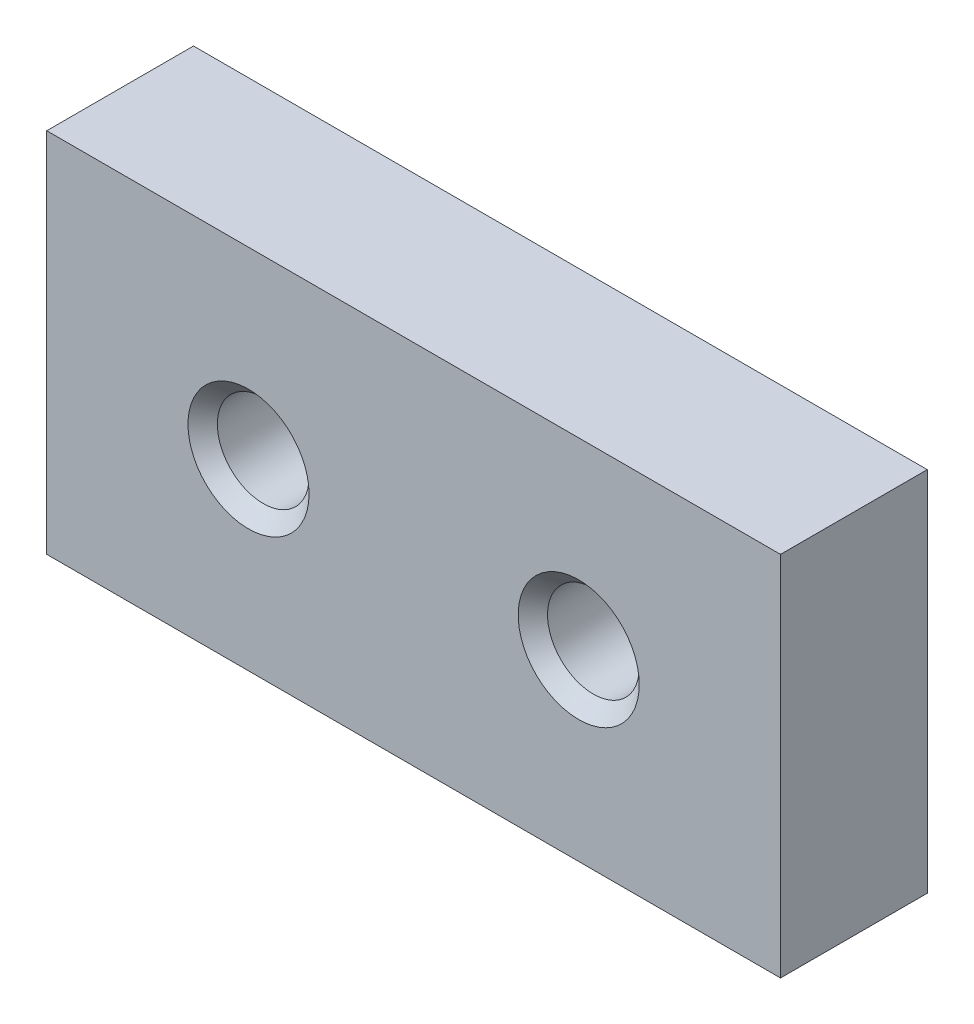
SolidWorks part; units mm, degrees
ref_plane "Спереди" through (0, 0, 0) normal (0, 0, 1) x (1, 0, 0)
ref_plane "Сверху" through (0, 0, 0) normal (0, 1, 0) x (1, 0, 0)
ref_plane "Справа" through (0, 0, 0) normal (1, 0, 0) x (0, 0, -1)
sketch "Эскиз1" plane through (0, 0, 0) normal (0, 0, 1) x (1, 0, 0)
  line L1 (-10, -5) -> (10, -5)
  line L2 (-10, -5) -> (-10, 5)
  line L3 (-10, 5) -> (10, 5)
  line L4 (10, -5) -> (10, 5)
  line L5 (-10, -5) -> (10, 5) construction
  line L6 (-10, 5) -> (10, -5) construction
  point P0 (0, 0)
  dimension "D1" = 10
  dimension "D2" = 20
extrude "Бобышка-Вытянуть1" add sketch "Эскиз1" along normal blind 4
hole_wizard "Отверстие обработанное метчиком M3x0.51" positions "Эскиз3" profile "Эскиз2" tap size "M3x0.5" standard "Ansi (метрические)" end condition through all
sketch "Эскиз3" plane through (0, 0, 4) normal (0, 0, 1) x (1, 0, 0)
  line L0 (-10, 5) -> (-10, -5) construction
  point P0 (-4.5, 0)
  point P1 (4.5, 0)
  dimension "D1" = 9
  dimension "D2" = 5.5
sketch "Эскиз2" plane through (-4.5, 0, 4) normal (1, 0, 0) x (0, -1, 0)
  line L0 (0, 0) -> (0, 4)
  line L1 (0, 4) -> (1.65, 4)
  line L2 (1.25, 3.6) -> (1.25, 0.4)
  line L3 (1.25, 0.4) -> (1.65, 0)
  line L5 (1.65, 0) -> (0, 0)
  line L6 (-1.25, 0.4) -> (-1.65, 0) construction
  line L7 (1.65, 4) -> (1.25, 3.6)
  line L8 (-1.65, 4) -> (-1.25, 3.6) construction
  line L11 (0, -6.35) -> (0, 107.95) construction
  dimension "Диаметр проходного сверла" = 2.5
  dimension "Глубина проходного сверла" = 4
  dimension "Диаметр передней зенковки" = 3.3
  dimension "Угол передней зенковки" = 90
  dimension "Диаметр задней зенковки" = 3.3
  dimension "Угол задней зенковки" = 90
cosmetic thread "Отверстие резьбы1"
cosmetic thread "Отверстие резьбы2"
